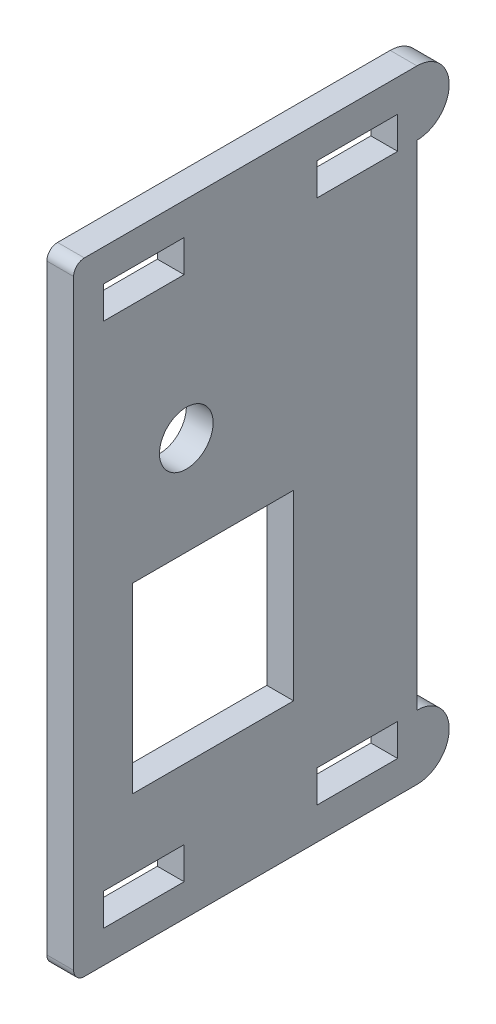
SolidWorks part; units mm, degrees
ref_plane "前视" through (0, 0, 0) normal (0, 0, 1) x (1, 0, 0)
ref_plane "上视" through (0, 0, 0) normal (0, 1, 0) x (1, 0, 0)
ref_plane "右视" through (0, 0, 0) normal (1, 0, 0) x (0, 0, -1)
sketch "草图2" plane through (0, 0, 0) normal (1, 0, 0) x (0, 0, -1)
  line L1 (-17.5, 29) -> (17.5, 29)
  line L2 (-17.5, 29) -> (-17.5, -29)
  line L3 (-17.5, -29) -> (17.5, -29)
  line L4 (17.5, 29) -> (17.5, -29)
  line L5 (-17.5, 29) -> (17.5, -29) construction
  line L6 (-17.5, -29) -> (17.5, 29) construction
  point P0 (0, 0)
  dimension "D1" = 58
  dimension "D2" = 35
extrude "凸台-拉伸1" add sketch "草图2" along normal blind 2.5
sketch "草图4" plane through (0, 0, 0) normal (-1, 0, 0) x (0, 0, 1)
  line L0 (-17.8855, 26) -> (19.6323, 26) construction
  line L1 (-17.5, 29) -> (17.5, 29) construction
  line L2 (-12.7, 26) -> (-5.2, 26)
  line L3 (-5.2, 26) -> (-5.2, 23)
  line L4 (-5.2, 23) -> (-12.7, 23)
  line L5 (-12.7, 23) -> (-12.7, 26)
  line L6 (-17.5, -29) -> (-17.5, 29) construction
  line L7 (7.2, 26) -> (14.7, 26)
  line L8 (14.7, 26) -> (14.7, 23)
  line L9 (14.7, 23) -> (7.2, 23)
  line L10 (7.2, 23) -> (7.2, 26)
  line L11 (17.5, 29) -> (17.5, -29) construction
  line L12 (0, 0) -> (-2.7087, 0) construction
  line L13 (-12.7, -23) -> (-12.7, -26)
  line L14 (7.2, -23) -> (7.2, -26)
  line L15 (-5.2, -26) -> (-5.2, -23)
  line L16 (14.7, -26) -> (14.7, -23)
  line L17 (14.7, -23) -> (7.2, -23)
  line L18 (7.2, -26) -> (14.7, -26)
  line L19 (-12.7, -26) -> (-5.2, -26)
  line L20 (-5.2, -23) -> (-12.7, -23)
  dimension "D1" = 3
  dimension "D2" = 4.8
  dimension "D3" = 3
  dimension "D4" = 7.5
  dimension "D5" = 7.5
  dimension "D6" = 3
  dimension "D7" = 2.8
extrude "切除-拉伸1" cut sketch "草图4" against normal through all
sketch "草图5" plane through (0, 0, 0) normal (-1, 0, 0) x (0, 0, 1)
  line L0 (-13.8103, 26) -> (-12.7631, 26) construction
  line L1 (-17.5, 29) -> (17.5, 29) construction
  line L2 (-14.5, 27.3502) -> (-14.5, 25.8843) construction
  line L3 (-17.5, -29) -> (-17.5, 29) construction
  line L4 (-11.0063, 0) -> (-20.4085, 0) construction
  line L5 (-14.5, 23) -> (-14.5, -23)
  line L6 (-14.5, 0) -> (-17.5, 0)
  line L7 (-17.5, -29) -> (-17.5, 29)
  line L8 (-14.5, 29) -> (-17.5, 29)
  line L9 (0, 0) -> (-4.681, 0) construction
  line L10 (-14.5, -29) -> (-17.5, -29)
  arc A0 (-14.5, 29) -> (-14.5, 23) centre (-14.5, 26) ccw
  arc A1 (-14.5, -29) -> (-14.5, -23) centre (-14.5, -26) cw
  line M9 (-17.5, 29) -> (-17.5, -29)
  line M10 (-17.5, -29) -> (17.5, -29)
  line M12 (17.5, 29) -> (-17.5, 29)
  dimension "D1" = 3
  dimension "D2" = 3
extrude "切除-拉伸2" cut sketch "草图5" against normal through all contours A0 M12 M9 | A0 L7 L6 L5 | A1 L5 L6 M9 | A1 L7 M10
sketch "草图7" plane through (0, 0, 0) normal (-1, 0, 0) x (0, 0, 1)
  line L0 (-12.7, -26) -> (-5.2, -26) construction
  line L1 (-3, 0.5) -> (12, 0.5)
  line L2 (-3, 0.5) -> (-3, -16.5)
  line L3 (-3, -16.5) -> (12, -16.5)
  line L4 (12, 0.5) -> (12, -16.5)
  line L5 (-14.5, 23) -> (-14.5, -23) construction
  line L6 (0, 0) -> (-3.3542, 0) construction
  circle A0 centre (7, 9.7) radius 2.5
  dimension "D7" = 5
  dimension "D1" = 9.5
  dimension "D2" = 17
  dimension "D3" = 15
  dimension "D4" = 11.5
  dimension "D5" = 9.2
  dimension "D6" = 21.5
extrude "切除-拉伸3" cut sketch "草图7" against normal through all
fillet "圆角1" radius 1 2 edges at (1.25, -29, 17.5) (1.25, 29, 17.5)
